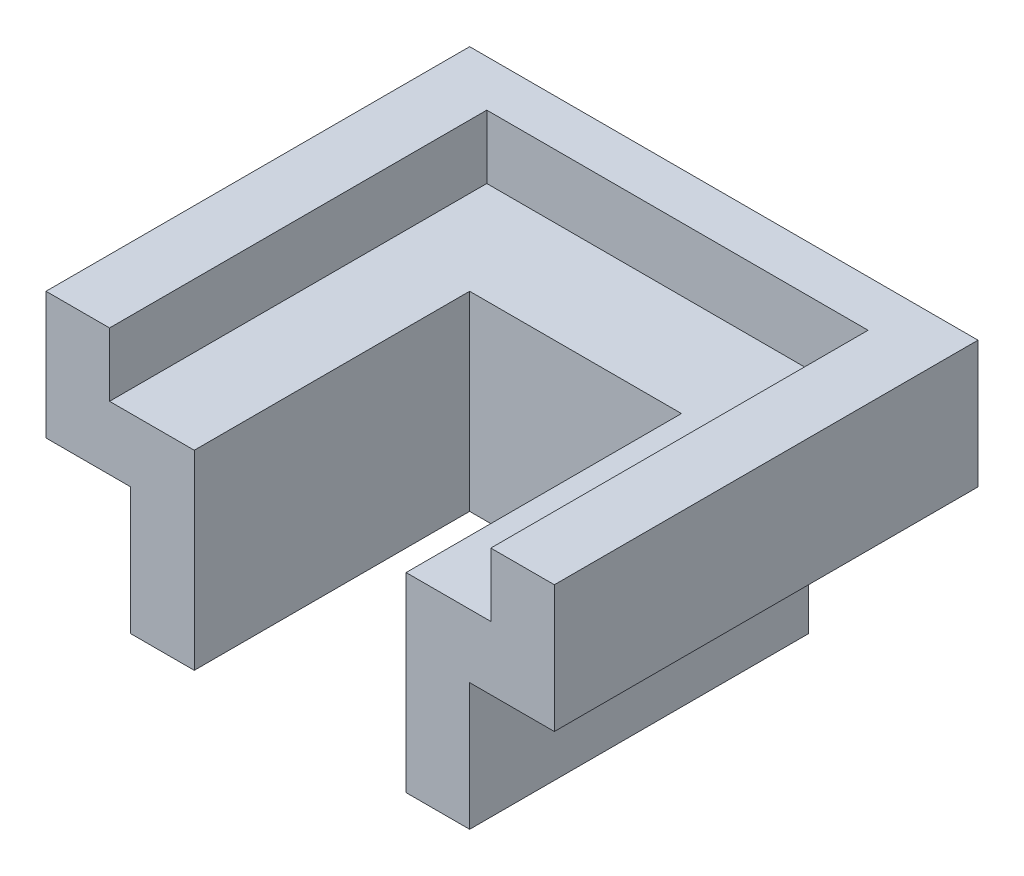
SolidWorks part; units mm, degrees
ref_plane "Front Plane" through (0, 0, 0) normal (0, 0, 1) x (1, 0, 0)
ref_plane "Top Plane" through (0, 0, 0) normal (0, 1, 0) x (1, 0, 0)
ref_plane "Right Plane" through (0, 0, 0) normal (1, 0, 0) x (0, 0, -1)
sketch "Sketch1" plane through (0, 0, 0) normal (1, 0, 0) x (0, 0, -1)
  line L1 (-12.2248, -8.4019) -> (51.2752, -8.4019)
  line L2 (-12.2248, -8.4019) -> (-12.2248, 10.6481)
  line L3 (-12.2248, 10.6481) -> (51.2752, 10.6481)
  line L4 (51.2752, -8.4019) -> (51.2752, 10.6481)
  dimension "D1" = 19.05
  dimension "D2" = 63.5
extrude "Boss-Extrude1" add sketch "Sketch1" along normal mid plane 76.2
sketch "Sketch2" plane through (0, 10.6481, 0) normal (0, 1, 0) x (1, 0, 0)
  line L0 (38.1, -12.2248) -> (-38.1, -12.2248) construction
  line L1 (-28.575, -12.2248) -> (28.575, -12.2248)
  line L2 (-28.575, -12.2248) -> (-28.575, 44.3217)
  line L3 (-28.575, 44.3217) -> (28.575, 44.3217)
  line L4 (28.575, -12.2248) -> (28.575, 44.3217)
  line L5 (-38.1, 51.2752) -> (-38.1, -12.2248) construction
  line L6 (0, -10.4775) -> (0, 10.4775) construction
  point P8 (0, -12.2248)
  dimension "D1" = 9.525
extrude "Cut-Extrude1" cut sketch "Sketch2" against normal blind 9.525
sketch "Sketch5" plane through (0, -8.4019, 0) normal (0, -1, 0) x (1, 0, 0)
  line L0 (-25.4, 12.2248) -> (-15.875, 12.2248)
  line L1 (38.1, 12.2248) -> (-38.1, 12.2248) construction
  line L2 (-15.875, 12.2248) -> (-15.875, -29.0502)
  line L3 (-15.875, -29.0502) -> (15.875, -29.0502)
  line L4 (15.875, -29.0502) -> (15.875, 12.2248)
  line L5 (15.875, 12.2248) -> (25.4, 12.2248)
  line L6 (25.4, 12.2248) -> (25.4, -38.5752)
  line L7 (-25.4, -38.5752) -> (25.4, -38.5752)
  line L8 (-25.4, 12.2248) -> (-25.4, -38.5752)
  line L9 (38.1, -51.2752) -> (-38.1, -51.2752) construction
  line L10 (0, -10.4775) -> (0, 10.4775) construction
  point P4 (0, -38.5752)
  point P13 (0, -51.2752)
  point P14 (0, -29.0502)
  point P15 (0, -38.5752)
  dimension "D1" = 9.525
  dimension "D2" = 31.75
  dimension "D3" = 50.8
  dimension "D4" = 9.525
extrude "Boss-Extrude3" add sketch "Sketch5" along normal blind 19.05
sketch "Sketch6" plane through (0, -8.4019, 0) normal (0, -1, 0) x (1, 0, 0)
  line L1 (-15.875, 12.2248) -> (15.875, 12.2248)
  line L2 (-15.875, 12.2248) -> (-15.875, -29.0502)
  line L3 (-15.875, -29.0502) -> (15.875, -29.0502)
  line L4 (15.875, 12.2248) -> (15.875, -29.0502)
extrude "Cut-Extrude3" cut sketch "Sketch6" against normal blind 19.05
